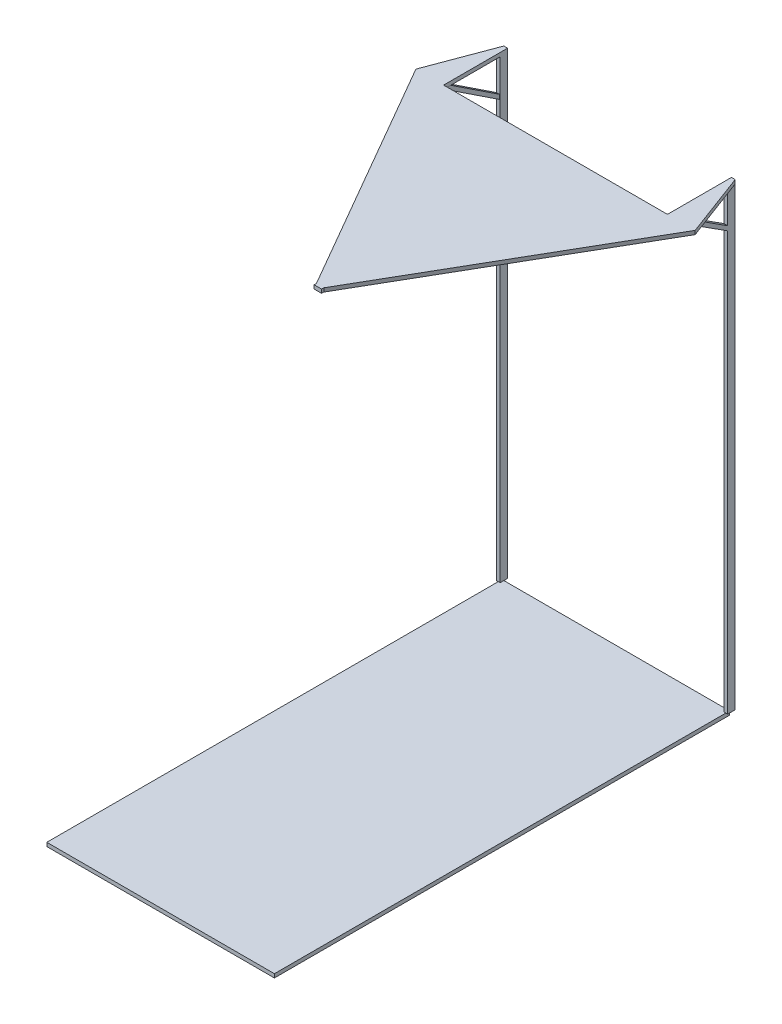
SolidWorks part; units mm, degrees
ref_plane "Front Plane" through (0, 0, 0) normal (0, 0, 1) x (1, 0, 0)
ref_plane "Top Plane" through (0, 0, 0) normal (0, 1, 0) x (1, 0, 0)
ref_plane "Right Plane" through (0, 0, 0) normal (1, 0, 0) x (0, 0, -1)
sketch "Sketch2" plane through (0, 0, 0) normal (0, 1, 0) x (1, 0, 0)
  line L1 (-152.4, 304.8) -> (152.4, 304.8)
  line L2 (-152.4, 304.8) -> (-152.4, -304.8)
  line L3 (-152.4, -304.8) -> (152.4, -304.8)
  line L4 (152.4, 304.8) -> (152.4, -304.8)
  line L5 (-152.4, 304.8) -> (152.4, -304.8) construction
  line L6 (-152.4, -304.8) -> (152.4, 304.8) construction
  point P0 (0, 0)
  dimension "D1" = 304.8
  dimension "D2" = 609.6
extrude "Boss-Extrude1" add sketch "Sketch2" along normal blind 5
sketch "Sketch3" plane through (152.4, 0, 0) normal (1, 0, 0) x (0, 0, -1)
  line L0 (-304.8, 5) -> (-304.8, 615)
  line L1 (304.8, 5) -> (304.8, 615)
  dimension "D1" = 610
extrude "Extrude-Thin1" add sketch "Sketch3" along normal mid plane 5 thin contours L0 | L1 thin type mid plane wall 10
sketch "Sketch4" plane through (-152.4, 0, 0) normal (-1, 0, 0) x (0, 0, 1)
  line L0 (-304.8, 5) -> (-304.8, 615)
  line L1 (304.8, 5) -> (304.8, 615)
  dimension "D1" = 610
  dimension "D2" = 610
extrude "Extrude-Thin2" add sketch "Sketch4" along normal mid plane 5 thin thin type mid plane wall 10
sketch "Sketch5" plane through (0, 615, 0) normal (0, 1, 0) x (1, 0, 0)
  line L0 (154.9, -309.8) -> (-154.9, -309.8)
  line L1 (-154.9, -309.8) -> (-154.9, -299.8)
  line L2 (-154.9, -299.8) -> (-5, -299.8)
  line L3 (154.9, -299.8) -> (154.9, -309.8)
  line L4 (5, -299.8) -> (154.9, -299.8)
  line L6 (5, -104.7875) -> (5, -299.8)
  line L7 (-5, -99.8) -> (-5, -91.1335)
  line L9 (-5, -99.8) -> (-5, -299.8)
  line L11 (187, 224.0998) -> (5, -91.1335)
  line L12 (-187, 224.0998) -> (-5, -91.1335)
  line L16 (0, -309.8) -> (0, -99.7937) construction
  line L18 (5, -91.1335) -> (5, -104.7875)
  line L24 (-154.9, 309.8) -> (-149.9, 309.8)
  line L30 (154.9, 309.8) -> (149.9, 309.8)
  line L32 (-149.9, 224.0998) -> (149.9, 224.0998)
  line L33 (-154.9, 309.8) -> (-187, 224.0998)
  line L34 (187, 224.0998) -> (154.9, 309.8)
  line L35 (149.9, 309.8) -> (149.9, 224.0998)
  line L36 (-149.9, 224.0998) -> (-149.9, 309.8)
  point P17 (-0.0186, 164.3272)
  point P20 (0, 224.0998)
  dimension "D1" = 200
  dimension "D3" = 374
  dimension "D4" = 374
  dimension "D5" = 374
extrude "Boss-Extrude2" add sketch "Sketch5" along normal blind 5
sketch "Sketch6" plane through (-154.9, 0, 0) normal (-1, 0, 0) x (0, 0, 1)
  line L0 (-224.0998, 615) -> (-299.8, 565)
  line L1 (-299.8, 5) -> (-299.8, 615) construction
  dimension "D1" = 50
extrude "Extrude-Thin3" add sketch "Sketch6" against normal blind 4 thin
sketch "Sketch11" plane through (154.9, 0, 0) normal (1, 0, 0) x (0, 0, -1)
  line L0 (224.0998, 620) -> (309.8, 565)
  line L1 (309.8, 5) -> (309.8, 615) construction
  dimension "D1" = 50
extrude "Extrude-Thin5" add sketch "Sketch11" against normal blind 5 thin
sketch "Sketch12" plane through (0, 620, 0) normal (0, 1, 0) x (1, 0, 0)
  line L2 (-154.9, -94.1431) -> (154.9, -94.1431)
  line L4 (-154.9, -94.1431) -> (-154.9, -309.8)
  line L5 (-154.9, -309.8) -> (154.9, -309.8)
  line L6 (154.9, -309.8) -> (154.9, -94.1431)
  point P10 (0, 0)
extrude "Cut-Extrude1" cut sketch "Sketch12" against normal blind 615 contours L6 L2 L4 L5
